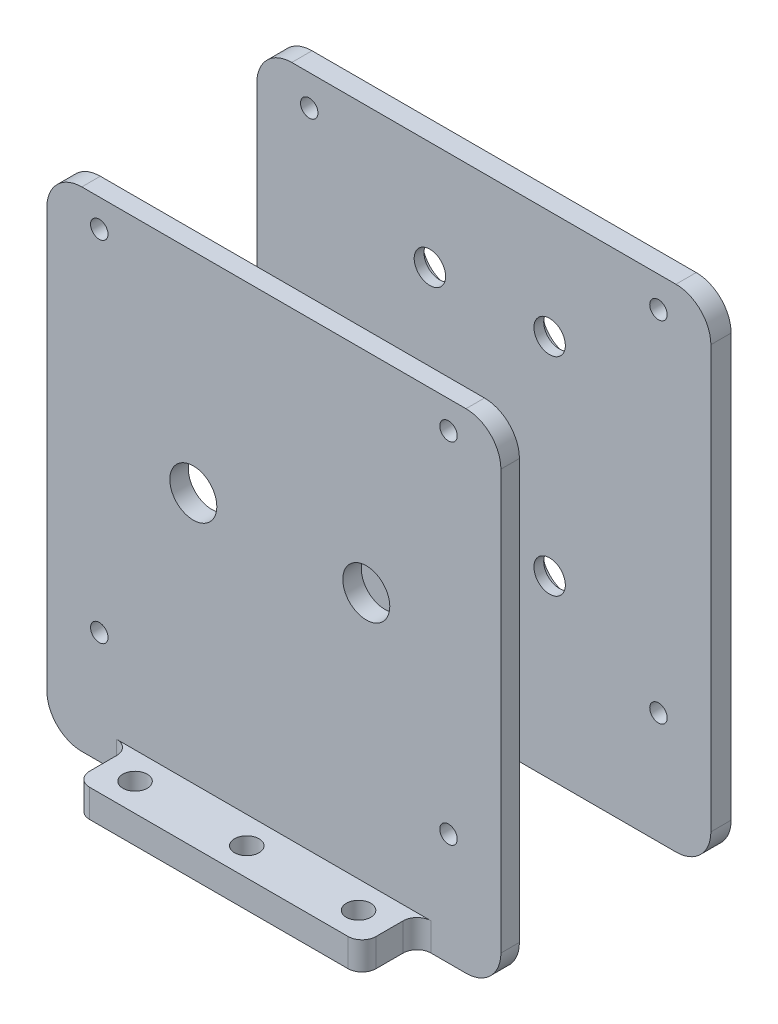
SolidWorks part; units mm, degrees
ref_plane "Front Plane" through (0, 0, 0) normal (0, 0, 1) x (1, 0, 0)
ref_plane "Top Plane" through (0, 0, 0) normal (0, 1, 0) x (1, 0, 0)
ref_plane "Right Plane" through (0, 0, 0) normal (1, 0, 0) x (0, 0, -1)
sketch "Sketch1" plane through (0, 0, 0) normal (0, 0, 1) x (1, 0, 0)
  line L0 (0, 4) -> (0, 0) construction
  line L1 (-32.5, 35) -> (32.5, 35)
  line L2 (-32.5, 35) -> (-32.5, -35)
  line L3 (-32.5, -35) -> (32.5, -35)
  line L4 (32.5, 35) -> (32.5, -35)
  line L5 (-32.5, 35) -> (32.5, -35) construction
  line L6 (-32.5, -35) -> (32.5, 35) construction
  line L7 (25, -21) -> (-25, -21) construction
  line L8 (25, -21) -> (25, 29) construction
  line L9 (25, 29) -> (-25, 29) construction
  line L10 (-25, -21) -> (-25, 29) construction
  line L11 (25, -21) -> (-25, 29) construction
  line L12 (25, 29) -> (-25, -21) construction
  point P0 (0, 0)
  point P6 (0, 4)
  dimension "D1" = 70
  dimension "D2" = 65
  dimension "D4" = 50
  dimension "D5" = 6
extrude "Boss-Extrude1" add sketch "Sketch1" along normal blind 2.65
fillet "Fillet1" radius 5 4 edges at (32.5, -35, 1.325) (-32.5, -35, 1.325) (32.5, 35, 1.325) (-32.5, 35, 1.325)
sketch "Sketch2" plane through (0, 0, 2.65) normal (0, 0, 1) x (1, 0, 0)
  line L0 (-27.5, -35) -> (27.5, -35) construction
  line L1 (-20.5, -35) -> (20.5, -35)
  line L2 (-20.5, -35) -> (-20.5, -31)
  line L3 (-20.5, -31) -> (20.5, -31)
  line L4 (20.5, -35) -> (20.5, -31)
  line L5 (0, 0) -> (0, -31) construction
  dimension "D1" = 41
  dimension "D2" = 4
extrude "Boss-Extrude2" add sketch "Sketch2" along normal blind 7.8799
fillet "Fillet2" radius 2 4 edges at (20.5, -33, 2.65) (20.5, -33, 10.5299) (-20.5, -33, 10.5299) (-20.5, -33, 2.65)
sketch "草图1" plane through (0, -35, 0) normal (0, -1, 0) x (1, 0, 0)
  line L0 (-16, 6.5299) -> (0, 6.5299) construction
  line L1 (0, 6.5299) -> (16, 6.5299) construction
  line L2 (-18.5, 10.5299) -> (18.5, 10.5299) construction
  circle A0 centre (-16, 6.5299) radius 1.75
  circle A1 centre (0, 6.5299) radius 1.75
  circle A2 centre (16, 6.5299) radius 1.75
  dimension "D2" = 3.5
  dimension "D1" = 16
  dimension "D3" = 4
extrude "切除-拉伸1" cut sketch "草图1" against normal through all
sketch "草图2" plane through (0, 0, 0) normal (0, 0, -1) x (-1, 0, 0)
  line L0 (-25, 31) -> (25, -19) construction
  line L1 (-25, 31) -> (25, 31) construction
  line L2 (-25, 31) -> (-25, -19) construction
  line L3 (-25, -19) -> (25, -19) construction
  line L4 (25, 31) -> (25, -19) construction
  line L5 (-27.5, 35) -> (27.5, 35) construction
  point P4 (0, 6)
  point P8 (0, 35)
  dimension "D1" = 50
  dimension "D2" = 50
  dimension "D3" = 4
hole_wizard "M3 螺纹孔1" positions "3D草图1" profile "草图3" tap size "M3" standard "ISO"
sketch3d "3D草图1"
  point P0 (25, -19, 0)
  point P3 (25, 31, 0)
  point P6 (-25, 31, 0)
  point P9 (-25, -19, 0)
sketch "草图3" plane through (25, -19, 0) normal (1, 0, 0) x (0, 1, 0)
  line L0 (0, 0) -> (0, 10.7511)
  line L1 (0, 10.7511) -> (1.25, 10)
  line L2 (1.25, 10) -> (1.25, 0)
  line L5 (1.25, 0) -> (0, 0)
  line L10 (0, 10.7511) -> (-1.25, 10) construction
  line L11 (0, -6.35) -> (0, 107.95) construction
  dimension "螺纹孔钻头直径" = 2.5
  dimension "螺纹孔钻头深度" = 10
  dimension "导头角度" = 118
cosmetic thread "孔螺蚊线1" parameters "D1"=6, "D2"=3
cosmetic thread "孔螺蚊线2" parameters "D1"=6, "D2"=3
cosmetic thread "孔螺蚊线3" parameters "D1"=6, "D2"=3
cosmetic thread "孔螺蚊线4" parameters "D1"=6, "D2"=3
sketch "草图8" plane through (0, 0, 0) normal (0, 0, -1) x (-1, 0, 0)
  circle A0 centre (11.5372, 5.028) radius 3.3655
extrude "切除-拉伸2" cut sketch "草图8" against normal up to next contours A0
sketch "草图10" plane through (0, 0, 0) normal (0, 0, -1) x (-1, 0, 0)
  circle A0 centre (-13.2278, 5.028) radius 3.3655
extrude "切除-拉伸3" cut sketch "草图10" against normal up to next
ref_plane "基准面1" through (0, 0, -30.31) normal (0, 0, -1) x (-1, 0, 0)
sketch "草图11" plane through (0, 0, -30.31) normal (0, 0, -1) x (-1, 0, 0)
  line L0 (-32.5, 34.15) -> (-32.5, 36.65) construction
  line L1 (32.5, -35) -> (-32.5, -35)
  line L2 (32.5, -35) -> (32.5, 35.4)
  line L3 (32.5, 35.4) -> (-32.5, 35.4)
  line L4 (-32.5, -35) -> (-32.5, 35.4)
extrude "凸台-拉伸1" add sketch "草图11" against normal blind 2.9 separate body
fillet "圆角2" radius 5 1 edges at (-32.5, 35.4, -28.86)
fillet "圆角3" radius 5 1 edges at (-32.5, -35, -28.86)
fillet "圆角4" radius 5 1 edges at (32.5, -35, -28.86)
fillet "圆角5" radius 5 1 edges at (32.5, 35.4, -28.86)
sketch "草图15" plane through (0, 0, -30.31) normal (0, 0, -1) x (-1, 0, 0)
  circle A0 centre (-25, -19) radius 1.7
  circle A1 centre (-25, 31) radius 1.7
  circle A2 centre (25, -19) radius 1.7
  circle A3 centre (25, 31) radius 1.7
hole_wizard "M3 螺纹孔2" positions "草图23" profile "草图24" tap size "M3" standard "ISO" end condition up to next
sketch "草图23" plane through (0, 0, -30.31) normal (0, 0, -1) x (-1, 0, 0)
  point P0 (-25, 31)
  point P3 (25, 31)
  point P6 (-25, -19)
  point P9 (25, -19)
cosmetic thread "孔螺蚊线5" parameters "D2"=3
cosmetic thread "孔螺蚊线6" parameters "D2"=3
cosmetic thread "孔螺蚊线7" parameters "D2"=3
cosmetic thread "孔螺蚊线8" parameters "D2"=3
sketch "草图24" plane through (25, 31, -30.31) normal (1, 0, 0) x (0, 1, 0)
  line L0 (0, 0) -> (0, 2.901)
  line L1 (0, 2.901) -> (1.25, 2.901)
  line L2 (1.25, 2.901) -> (1.25, 0)
  line L5 (1.25, 0) -> (0, 0)
  line L11 (0, -6.35) -> (0, 107.95) construction
  dimension "通孔螺纹孔钻头直径" = 2.5
  dimension "通孔螺纹孔钻头深度" = 2.901
hole_wizard "M4 六角凹头螺钉的柱形沉头孔2" positions "草图26" profile "草图27" counterbore size "M4" standard "ISO" end condition up to next
sketch "草图26" plane through (0, 0, -30.31) normal (0, 0, -1) x (-1, 0, 0)
  point P0 (-9.4177, -9.82)
  point P3 (7.7273, -9.82)
  point P6 (7.7272, 19.876)
  point P9 (-9.4178, 19.876)
sketch "草图27" plane through (9.4177, -9.82, -30.31) normal (1, 0, 0) x (0, 1, 0)
  line L0 (0, 0) -> (0, 32.96)
  line L1 (0, 32.96) -> (2.25, 32.96)
  line L3 (2.25, 32.96) -> (2.25, 1.5)
  line L4 (2.25, 1.5) -> (4, 1.5)
  line L5 (4, 1.5) -> (4, 0)
  line L7 (4, 0) -> (0, 0)
  line L11 (0, -6.35) -> (0, 107.95) construction
  dimension "通孔孔直径" = 4.5
  dimension "通孔孔深度" = 32.96
  dimension "柱形沉头孔直径" = 8
  dimension "柱形沉头孔深度" = 1.5
